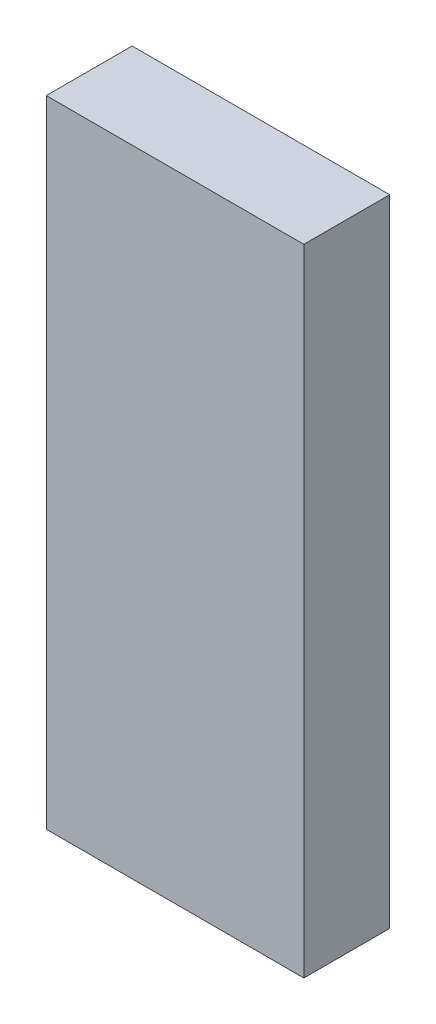
SolidWorks part; units mm, degrees
ref_plane "Front Plane" through (0, 0, 0) normal (0, 0, 1) x (1, 0, 0)
ref_plane "Top Plane" through (0, 0, 0) normal (0, 1, 0) x (1, 0, 0)
ref_plane "Right Plane" through (0, 0, 0) normal (1, 0, 0) x (0, 0, -1)
sketch "Sketch25" plane through (0, 0, 0) normal (0, 1, 0) x (1, 0, 0)
  line L1 (-19.05, -6.35) -> (19.05, -6.35)
  line L2 (-19.05, -6.35) -> (-19.05, 6.35)
  line L3 (-19.05, 6.35) -> (19.05, 6.35)
  line L4 (19.05, -6.35) -> (19.05, 6.35)
  line L5 (-19.05, -6.35) -> (19.05, 6.35) construction
  line L6 (-19.05, 6.35) -> (19.05, -6.35) construction
  point P0 (0, 0)
  dimension "D1" = 12.7
  dimension "D2" = 38.1
extrude "Boss-Extrude1" add sketch "Sketch25" along normal mid plane 93.98
hole_wizard "1/4-20 Tapped Hole1" [suppressed] positions "Sketch26" profile "Sketch27" tap size "1/4-20" standard "ANSI Inch"
sketch "Sketch26" plane through (0, 46.99, 0) normal (0, 1, 0) x (1, 0, 0)
  line L2 (-11.43, 0) -> (0, 0) construction
  line L3 (0, 0) -> (11.43, 0) construction
  point P2 (-11.43, 0)
  point P7 (11.43, 0)
  dimension "D1" = 22.86
sketch "Sketch27" plane through (-11.43, 46.99, 0) normal (1, 0, 0) x (0, 0, 1)
  line L0 (0, 0) -> (0, 18.0438)
  line L1 (0, 18.0438) -> (2.5527, 16.51)
  line L2 (2.5527, 16.51) -> (2.5527, 0)
  line L5 (2.5527, 0) -> (0, 0)
  line L10 (0, 18.0438) -> (-2.5527, 16.51) construction
  line L11 (0, -6.35) -> (0, 107.95) construction
  dimension "Tap Drill Dia." = 5.1054
  dimension "Tap Drill Depth" = 16.51
  dimension "Drill Angle" = 118
cosmetic thread "Hole Thread1" [suppressed] parameters "D1"=12.7, "D2"=6.35
cosmetic thread "Hole Thread2" [suppressed] parameters "D1"=12.7, "D2"=6.35
mirror "Mirror2" [suppressed] about plane through (0, 0, 0) normal (0, 1, 0)
sketch "Sketch28" plane through (0, 0, 6.35) normal (0, 0, 1) x (1, 0, 0)
  line L0 (0, 0) -> (0, -8.128) construction
  line L3 (0, 1.372) -> (0, -17.628) construction
  line L4 (-9.5, -8.128) -> (9.5, -8.128) construction
  circle A0 centre (0, -8.128) radius 9.5 construction
  dimension "D1" = 19
  dimension "D2" = 8.128
hole_wizard "M3 Clearance Hole2" [suppressed] positions "Sketch29" profile "Sketch30" hole size "M3" standard "ANSI Metric"
sketch "Sketch29" plane through (0, 0, 6.35) normal (0, 0, 1) x (1, 0, 0)
  point P0 (0, 1.372)
  point P3 (0, -17.628)
  point P6 (9.5, -8.128)
  point P9 (-9.5, -8.128)
sketch "Sketch30" plane through (0, 1.372, 6.35) normal (1, 0, 0) x (0, -1, 0)
  line L0 (0, 0) -> (0, 17.5915)
  line L1 (0, 17.5915) -> (1.8, 16.51)
  line L2 (1.8, 16.51) -> (1.8, 0)
  line L5 (1.8, 0) -> (0, 0)
  line L10 (0, 17.5915) -> (-1.8, 16.51) construction
  line L11 (0, -6.35) -> (0, 107.95) construction
  dimension "Hole Dia." = 3.6
  dimension "Hole Depth" = 16.51
  dimension "Drill Angle" = 118
sketch "Sketch31" plane through (0, 0, 6.35) normal (0, 0, 1) x (1, 0, 0)
  circle A0 centre (0, -8.128) radius 7.7
ref_point "Point1"
